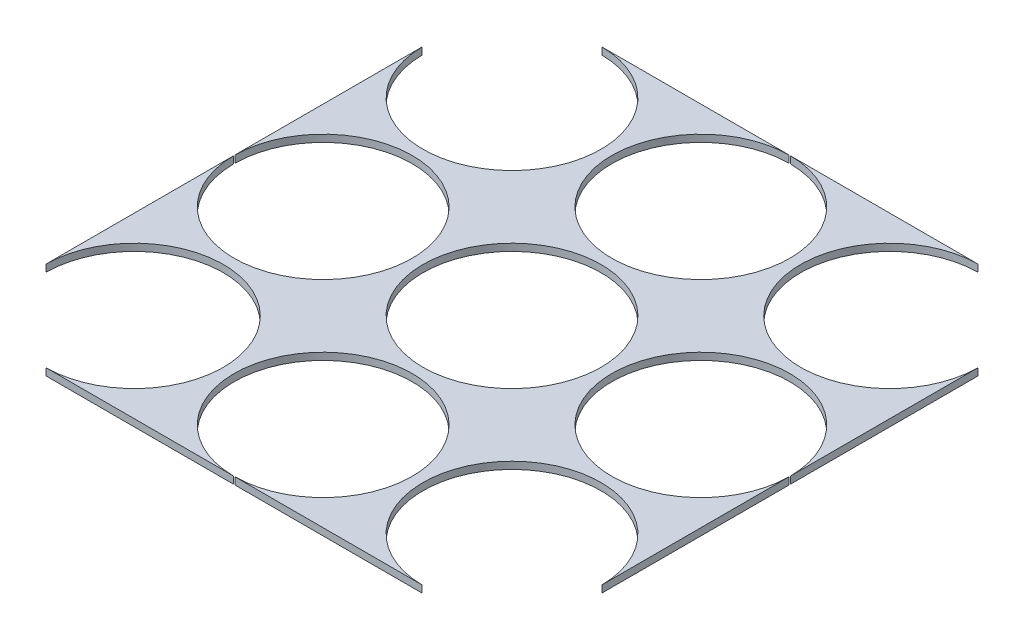
SolidWorks part; units mm, degrees
ref_plane "Front Plane" through (0, 0, 0) normal (0, 0, 1) x (1, 0, 0)
ref_plane "Top Plane" through (0, 0, 0) normal (0, 1, 0) x (1, 0, 0)
ref_plane "Right Plane" through (0, 0, 0) normal (1, 0, 0) x (0, 0, -1)
sketch "Sketch3" plane through (0, 0, 0) normal (0, 1, 0) x (1, 0, 0)
  line L1 (-123.825, -123.825) -> (123.825, -123.825)
  line L2 (-123.825, -123.825) -> (-123.825, 123.825)
  line L3 (-123.825, 123.825) -> (123.825, 123.825)
  line L4 (123.825, -123.825) -> (123.825, 123.825)
  line L5 (-123.825, -123.825) -> (123.825, 123.825) construction
  line L6 (-123.825, 123.825) -> (123.825, -123.825) construction
  point P0 (0, 0)
  dimension "D1" = 247.65
sketch "Sketch1" plane through (0, 0, 0) normal (0, 1, 0) x (1, 0, 0)
  line L0 (0, 0) -> (0, 140.1448) construction
  line L1 (-123.8263, -123.8263) -> (123.8263, -123.8263)
  line L2 (-123.8263, -123.8263) -> (-123.8263, 123.8263)
  line L3 (-123.8263, 123.8263) -> (123.8263, 123.8263)
  line L4 (123.8263, -123.8263) -> (123.8263, 123.8263)
  line L5 (-123.8263, -123.8263) -> (123.8263, 123.8263) construction
  line L6 (-123.8263, 123.8263) -> (123.8263, -123.8263) construction
  circle A9 centre (0, 0) radius 39.6875
  circle A10 centre (-84.1388, 0) radius 39.6875
  circle A11 centre (84.1388, 0) radius 39.6875
  circle A12 centre (-84.1388, 84.1388) radius 39.6875
  circle A13 centre (0, 84.1388) radius 39.6875
  circle A14 centre (84.1388, 84.1388) radius 39.6875
  circle A15 centre (-84.1388, -84.1388) radius 39.6875
  circle A16 centre (0, -84.1388) radius 39.6875
  circle A17 centre (84.1388, -84.1388) radius 39.6875
  point P0 (0, 0)
  dimension "D2" = 79.375
  dimension "D1" = 247.6525
  dimension "D4" = 2
  dimension "D3" = 2
extrude "Boss-Extrude5" add sketch "Sketch3" along normal blind 3.175
extrude "Cut-Extrude3" cut sketch "Sketch1" along normal through all contours A12 | A13 | A14 | A10 | A9 | A11 | A15 | A16 | A17 A15
